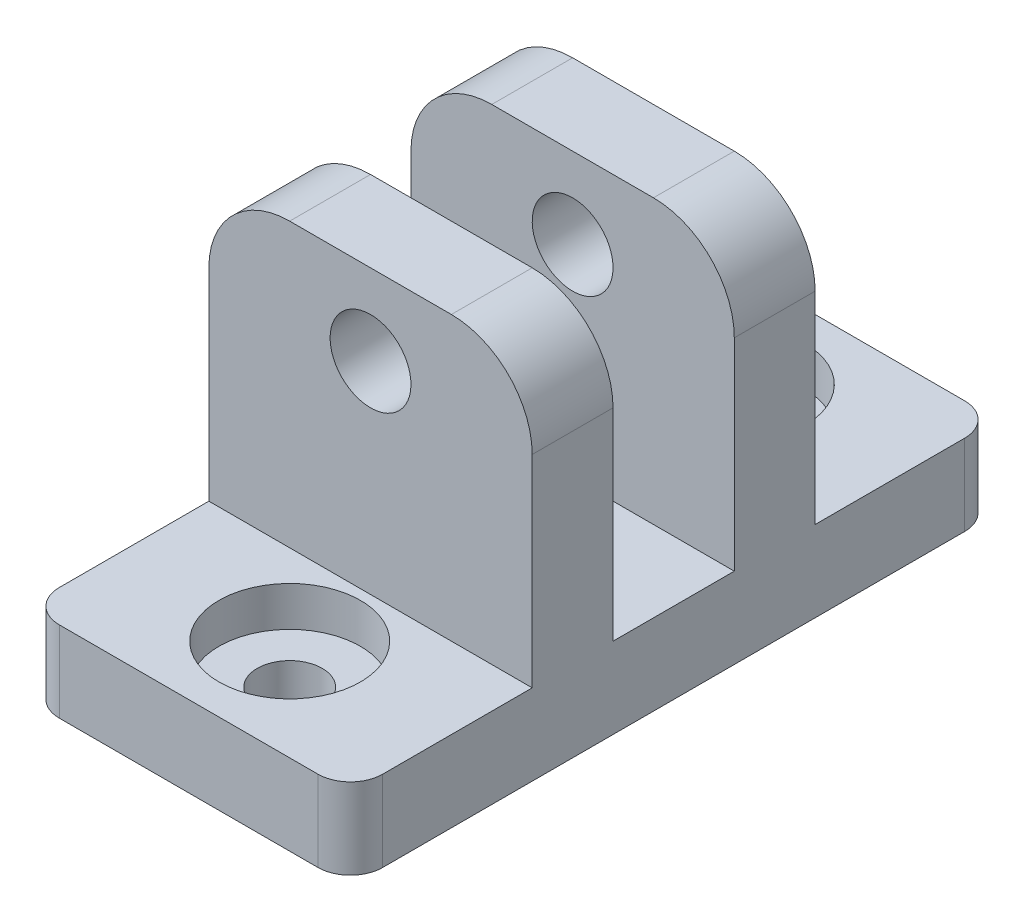
SolidWorks part; units mm, degrees
material "6061-T6 (SS)"
ref_plane "Front Plane" through (0, 0, 0) normal (0, 0, 1) x (1, 0, 0)
ref_plane "Top Plane" through (0, 0, 0) normal (0, 1, 0) x (1, 0, 0)
ref_plane "Right Plane" through (0, 0, 0) normal (1, 0, 0) x (0, 0, -1)
sketch "Sketch2" plane through (0, 0, 0) normal (0, 1, 0) x (1, 0, 0)
  line L1 (-12.7, -25.4) -> (12.7, -25.4)
  line L2 (-12.7, -25.4) -> (-12.7, 25.4)
  line L3 (-12.7, 25.4) -> (12.7, 25.4)
  line L4 (12.7, -25.4) -> (12.7, 25.4)
  line L5 (-12.7, -25.4) -> (12.7, 25.4) construction
  line L6 (-12.7, 25.4) -> (12.7, -25.4) construction
  point P0 (0, 0)
  dimension "D1" = 50.8
  dimension "D2" = 25.4
extrude "Boss-Extrude2" add sketch "Sketch2" along normal blind 28.575
sketch "Sketch3" plane through (12.7, 0, 0) normal (1, 0, 0) x (0, 0, -1)
  line L0 (-25.4, 28.575) -> (25.4, 28.575) construction
  line L1 (-25.4, 28.575) -> (-11.1125, 28.575)
  line L2 (-25.4, 28.575) -> (-25.4, 6.35)
  line L3 (-25.4, 6.35) -> (-11.1125, 6.35)
  line L4 (-11.1125, 28.575) -> (-11.1125, 6.35)
  line L5 (25.4, 28.575) -> (11.1125, 28.575)
  line L6 (25.4, 28.575) -> (25.4, 6.35)
  line L7 (25.4, 6.35) -> (11.1125, 6.35)
  line L8 (11.1125, 28.575) -> (11.1125, 6.35)
  line L9 (-4.7625, 28.575) -> (4.7625, 28.575)
  line L10 (-4.7625, 28.575) -> (-4.7625, 6.35)
  line L11 (-4.7625, 6.35) -> (4.7625, 6.35)
  line L12 (4.7625, 28.575) -> (4.7625, 6.35)
  line L13 (-25.4, 0) -> (25.4, 0) construction
  line L14 (0, 28.575) -> (0, 6.35) construction
  dimension "D1" = 6.35
  dimension "D2" = 6.35
  dimension "D3" = 9.525
extrude "Cut-Extrude1" cut sketch "Sketch3" against normal through all
sketch "Sketch5" plane through (0, 0, 25.4) normal (0, 0, 1) x (1, 0, 0)
  line L0 (-19.05, 28.575) -> (12.7, -9.525)
  line L5 (12.7, 6.35) -> (12.7, 28.575)
  line L6 (12.7, 28.575) -> (-12.7, 28.575)
  line L7 (-12.7, 28.575) -> (-12.7, 6.35)
  line L8 (-12.7, 6.35) -> (12.7, 6.35)
  line L9 (12.7, -9.525) -> (12.7, 28.575)
  line L10 (12.7, 28.575) -> (-19.05, 28.575)
  dimension "D2" = 31.75
  dimension "D3" = 38.1
  dimension "D1" = 0
hole_wizard "CBORE for #10 Binding Head Machine Screw1" positions "Sketch6" profile "Sketch7" counterbore size "#10" standard "ANSI Inch"
sketch "Sketch6" plane through (0, 6.35, 0) normal (0, 1, 0) x (1, 0, 0)
  line L0 (0, -17.4625) -> (0, 17.4625) construction
  point P130 (0, -17.4625)
  point P132 (0, 17.4625)
  point P137 (0, 0)
  dimension "D1" = 34.925
sketch "Sketch7" plane through (0, 6.35, 17.4625) normal (1, 0, 0) x (0, 0, 1)
  line L0 (0, 0) -> (0, 7.8838)
  line L1 (0, 7.8838) -> (2.5527, 6.35)
  line L2 (2.5527, 6.35) -> (2.5527, 3.1242)
  line L3 (2.5527, 3.1242) -> (5.5562, 3.1242)
  line L4 (5.5562, 3.1242) -> (5.5562, 0)
  line L5 (5.5562, 0) -> (0, 0)
  line L10 (0, 7.8838) -> (-2.5527, 6.35) construction
  line L11 (0, -6.35) -> (0, 107.95) construction
  dimension "Hole Dia." = 5.1054
  dimension "Hole Depth" = 6.35
  dimension "C'Bore Dia." = 11.1125
  dimension "C'Bore Depth" = 3.1242
  dimension "Drill Angle" = 118
sketch "Sketch8" plane through (0, 0, -11.1125) normal (0, 0, -1) x (-1, 0, 0)
  line L1 (12.7, 28.575) -> (-12.7, 28.575) construction
  line L2 (0, 22.225) -> (0, 28.575) construction
  line L3 (12.7, 28.575) -> (-12.7, 28.575) construction
  circle A0 centre (0, 22.225) radius 3.175
  dimension "D1" = 6.35
  dimension "D3" = 6.35
extrude "Cut-Extrude3" cut sketch "Sketch8" against normal through all
ref_plane "Plane2" through (0, 0, 0) normal (0, 0, -1) x (-1, 0, 0)
fillet "Fillet1" radius 6.35 4 edges at (12.7, 28.575, 7.9375) (12.7, 28.575, -7.9375) (-12.7, 28.575, -7.9375) (-12.7, 28.575, 7.9375)
fillet "Fillet2" radius 2.54 4 edges at (12.7, 3.175, 25.4) (12.7, 3.175, -25.4) (-12.7, 3.175, 25.4) (-12.7, 3.175, -25.4)
